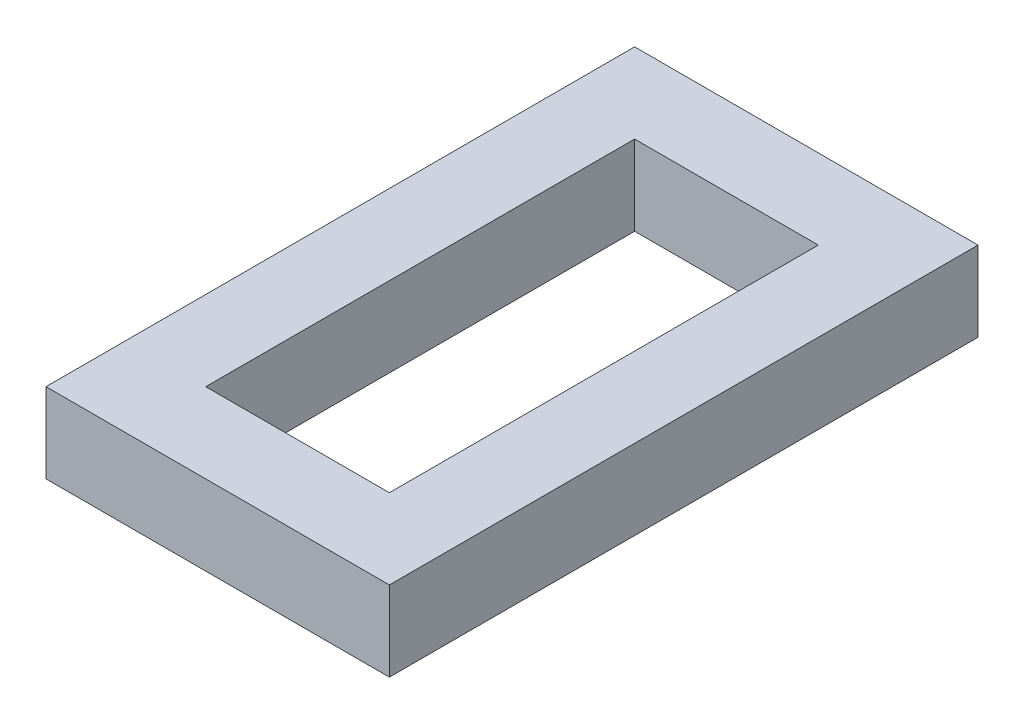
SolidWorks part; units mm, degrees
ref_plane "Front Plane" through (0, 0, 0) normal (0, 0, 1) x (1, 0, 0)
ref_plane "Top Plane" through (0, 0, 0) normal (0, 1, 0) x (1, 0, 0)
ref_plane "Right Plane" through (0, 0, 0) normal (1, 0, 0) x (0, 0, -1)
sketch "Sketch1" plane through (0, 0, 0) normal (0, 1, 0) x (1, 0, 0)
  line L0 (-18.25, -42.625) -> (-18.25, 42.625)
  line L1 (-34.125, -58.5) -> (34.125, -58.5)
  line L2 (-34.125, -58.5) -> (-34.125, 58.5)
  line L3 (-34.125, 58.5) -> (34.125, 58.5)
  line L4 (34.125, -58.5) -> (34.125, 58.5)
  line L5 (-34.125, -58.5) -> (34.125, 58.5) construction
  line L6 (-34.125, 58.5) -> (34.125, -58.5) construction
  line L7 (-18.25, 42.625) -> (18.25, 42.625)
  line L8 (18.25, -42.625) -> (18.25, 42.625)
  line L9 (-18.25, -42.625) -> (18.25, -42.625)
  point P0 (0, 0)
  dimension "D1" = 68.25
  dimension "D2" = 117
  dimension "D3" = 15.875
extrude "Boss-Extrude1" add sketch "Sketch1" along normal blind 15.875
